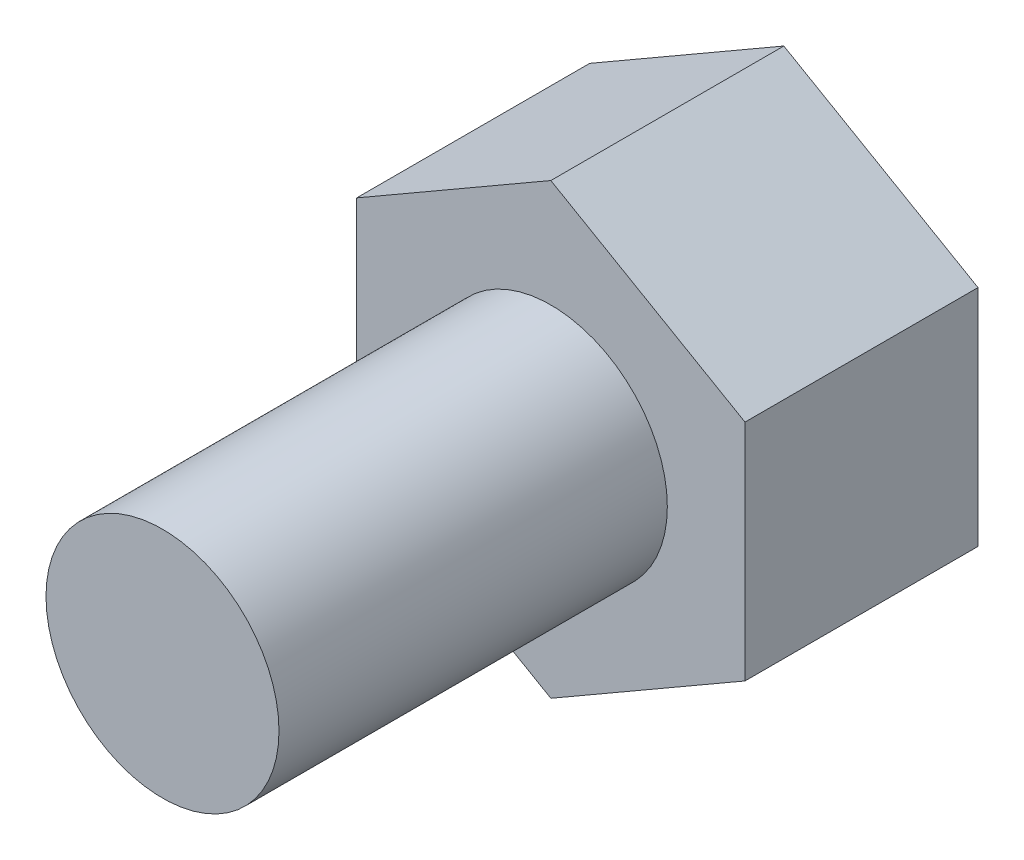
SolidWorks part; units mm, degrees
ref_plane "Front Plane" through (0, 0, 0) normal (0, 0, 1) x (1, 0, 0)
ref_plane "Top Plane" through (0, 0, 0) normal (0, 1, 0) x (1, 0, 0)
ref_plane "Right Plane" through (0, 0, 0) normal (1, 0, 0) x (0, 0, -1)
sketch "Sketch1" plane through (0, 0, 0) normal (0, 0, 1) x (1, 0, 0)
  circle A0 centre (-63.4948, 14.9787) radius 1.5
extrude "Boss-Extrude1" add sketch "Sketch1" along normal blind 5
sketch "Sketch2" plane through (0, 0, 0) normal (0, 0, -1) x (-1, 0, 0)
  line L1 (63.4948, 12.092) -> (65.9948, 13.5353)
  line L2 (65.9948, 13.5353) -> (65.9948, 16.4221)
  line L3 (65.9948, 16.4221) -> (63.4948, 17.8655)
  line L4 (63.4948, 17.8655) -> (60.9948, 16.4221)
  line L5 (60.9948, 16.4221) -> (60.9948, 13.5353)
  line L6 (60.9948, 13.5353) -> (63.4948, 12.092)
  circle A0 centre (63.4948, 14.9787) radius 2.5 construction
  dimension "D1" = 5
extrude "Boss-Extrude2" add sketch "Sketch2" along normal blind 3
